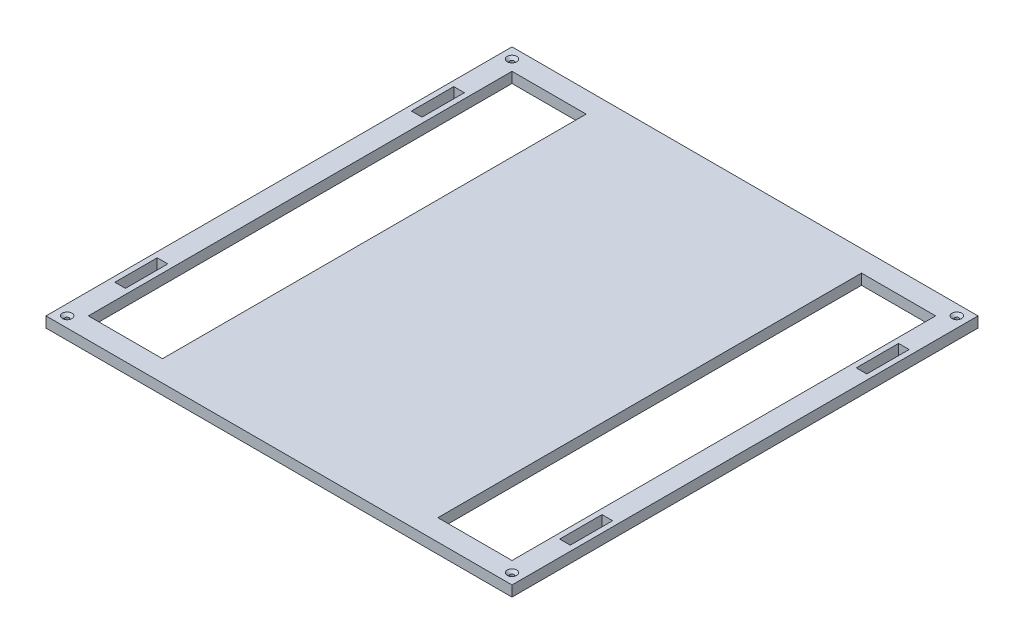
SolidWorks part; units mm, degrees
ref_plane "Front Plane" through (0, 0, 0) normal (0, 0, 1) x (1, 0, 0)
ref_plane "Top Plane" through (0, 0, 0) normal (0, 1, 0) x (1, 0, 0)
ref_plane "Right Plane" through (0, 0, 0) normal (1, 0, 0) x (0, 0, -1)
sketch "Sketch1" plane through (0, 0, 0) normal (0, 1, 0) x (1, 0, 0)
  line L1 (-139.7, 139.7) -> (139.7, 139.7)
  line L2 (-139.7, 139.7) -> (-139.7, -139.7)
  line L3 (-139.7, -139.7) -> (139.7, -139.7)
  line L4 (139.7, 139.7) -> (139.7, -139.7)
  line L5 (-139.7, 139.7) -> (139.7, -139.7) construction
  line L6 (-139.7, -139.7) -> (139.7, 139.7) construction
  point P0 (0, 0)
  dimension "D1" = 279.4
  dimension "D2" = 279.4
extrude "Boss-Extrude1" add sketch "Sketch1" along normal blind 6.35
sketch "Sketch2" plane through (0, 6.35, 0) normal (0, 1, 0) x (1, 0, 0)
  line L0 (-139.7, 0) -> (139.7, 0) construction
  line L1 (-127, 127) -> (-82.55, 127)
  line L2 (-127, 127) -> (-127, -127)
  line L3 (-127, -127) -> (-82.55, -127)
  line L4 (-82.55, 127) -> (-82.55, -127)
  line L5 (-139.7, 139.7) -> (-139.7, -139.7) construction
  line L6 (139.7, -139.7) -> (139.7, 139.7) construction
  line L7 (0, 139.7) -> (0, -139.7) construction
  line L8 (139.7, 139.7) -> (-139.7, 139.7) construction
  line L9 (-139.7, -139.7) -> (139.7, -139.7) construction
  line L10 (127, -127) -> (82.55, -127)
  line L11 (82.55, 127) -> (82.55, -127)
  line L12 (127, 127) -> (82.55, 127)
  line L13 (127, 127) -> (127, -127)
  line L14 (136.525, 76.2) -> (130.175, 76.2)
  line L15 (-136.525, 101.6) -> (-130.175, 101.6)
  line L16 (-136.525, 101.6) -> (-136.525, 76.2)
  line L17 (-136.525, 76.2) -> (-130.175, 76.2)
  line L18 (-130.175, 101.6) -> (-130.175, 76.2)
  line L19 (130.175, 101.6) -> (130.175, 76.2)
  line L20 (136.525, 101.6) -> (130.175, 101.6)
  line L21 (136.525, 101.6) -> (136.525, 76.2)
  line L22 (136.525, -101.6) -> (136.525, -76.2)
  line L23 (136.525, -101.6) -> (130.175, -101.6)
  line L24 (130.175, -101.6) -> (130.175, -76.2)
  line L25 (136.525, -76.2) -> (130.175, -76.2)
  line L26 (-136.525, -76.2) -> (-130.175, -76.2)
  line L27 (-130.175, -101.6) -> (-130.175, -76.2)
  line L28 (-136.525, -101.6) -> (-130.175, -101.6)
  line L29 (-136.525, -101.6) -> (-136.525, -76.2)
  point P10 (-82.55, 0)
  point P25 (-133.35, 101.6)
  dimension "D1" = 44.45
  dimension "D2" = 254
  dimension "D3" = 12.7
  dimension "D4" = 6.35
  dimension "D5" = 25.4
  dimension "D6" = 3.175
  dimension "D7" = 25.4
extrude "Cut-Extrude1" cut sketch "Sketch2" against normal through all
hole_wizard "#4-40 Tapped Hole1" positions "Sketch3" profile "Sketch4" tap size "#4-40" standard "ANSI Inch" end condition through all
sketch "Sketch3" plane through (0, 6.35, 0) normal (0, 1, 0) x (1, 0, 0)
  line L0 (139.7, 139.7) -> (-139.7, 139.7) construction
  line L1 (-139.7, 139.7) -> (-139.7, -139.7) construction
  line L2 (0, 139.7) -> (0, -139.7) construction
  line L3 (-139.7, -139.7) -> (139.7, -139.7) construction
  line L4 (-139.7, 0) -> (139.7, 0) construction
  line L5 (139.7, -139.7) -> (139.7, 139.7) construction
  point P0 (-133.35, 133.35)
  point P16 (-133.35, -133.35)
  point P17 (133.35, -133.35)
  point P18 (133.35, 133.35)
  dimension "D1" = 6.35
  dimension "D2" = 6.35
sketch "Sketch4" plane through (-133.35, 6.35, -133.35) normal (1, 0, 0) x (0, 0, 1)
  line L0 (0, 0) -> (0, 6.35)
  line L1 (0, 6.35) -> (1.1303, 6.35)
  line L2 (1.1303, 6.35) -> (1.1303, 1.4493)
  line L3 (1.1303, 1.4493) -> (2.8575, 0)
  line L5 (2.8575, 0) -> (0, 0)
  line L6 (-1.1303, 1.4493) -> (-2.8575, 0) construction
  line L11 (0, -6.35) -> (0, 107.95) construction
  dimension "Thread Major Dia." = 2.2606
  dimension "Thru Tap Drill Depth" = 6.35
  dimension "Near C'Sink Dia." = 5.715
  dimension "Near C'Sink Angle" = 100
